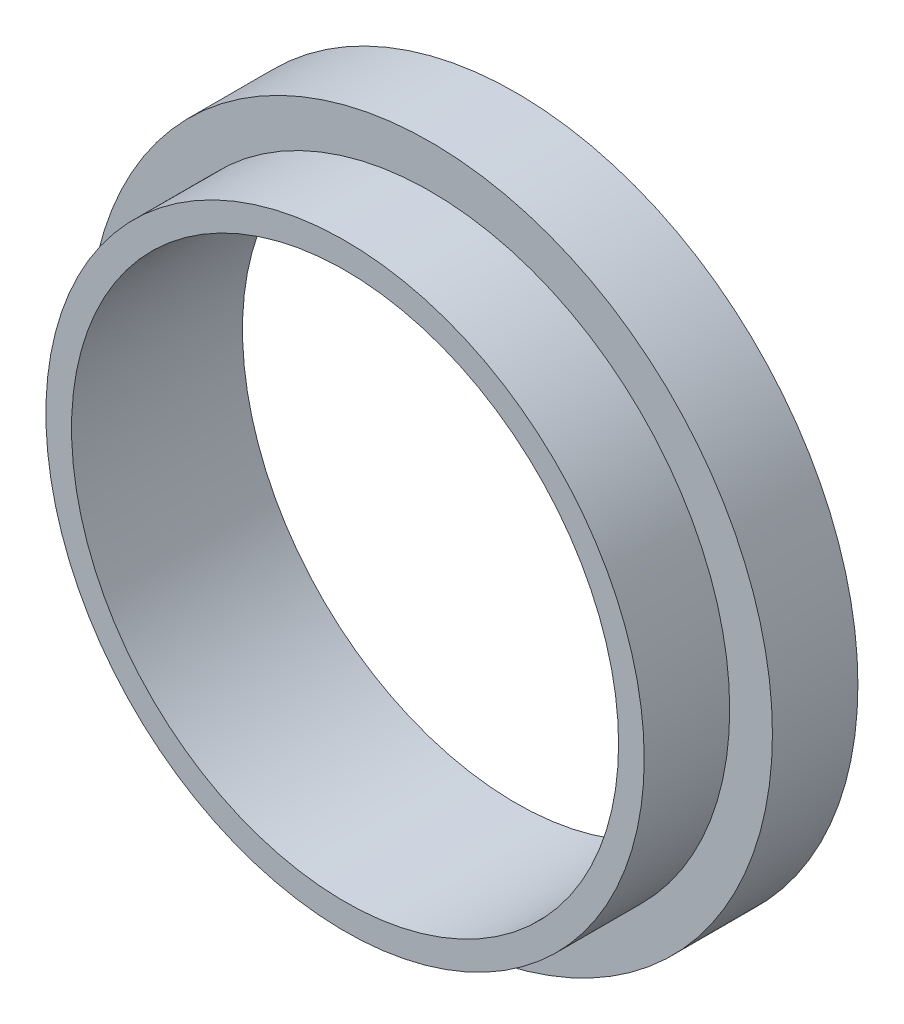
SolidWorks part; units mm, degrees
material "Nylon 101"
ref_plane "Front Plane" through (0, 0, 0) normal (0, 0, 1) x (1, 0, 0)
ref_plane "Top Plane" through (0, 0, 0) normal (0, 1, 0) x (1, 0, 0)
ref_plane "Right Plane" through (0, 0, 0) normal (1, 0, 0) x (0, 0, -1)
sketch "Sketch1" plane through (0, 0, 0) normal (0, 0, 1) x (1, 0, 0)
  circle A0 centre (0, 0) radius 32
  circle A1 centre (0, 0) radius 35
extrude "Boss-Extrude1" add sketch "Sketch1" along normal blind 10
sketch "Sketch2" plane through (0, 0, 0) normal (0, 0, 1) x (1, 0, 0)
  circle A0 centre (0, 0) radius 32
  circle A1 centre (0, 0) radius 40
extrude "Boss-Extrude2" add sketch "Sketch2" against normal blind 10
